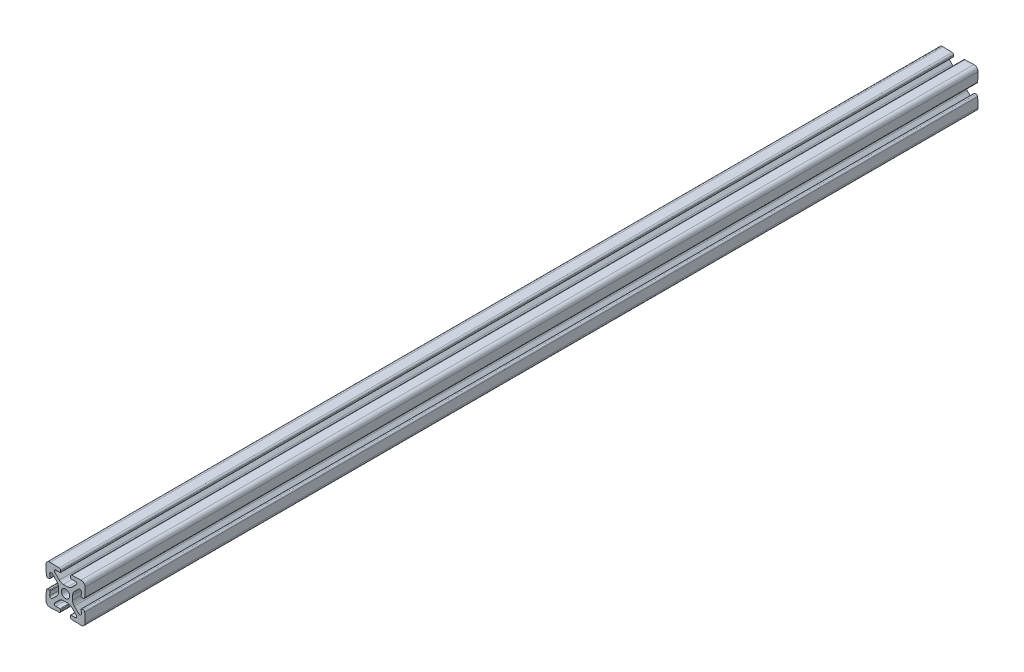
SolidWorks part; units mm, degrees
ref_plane "Front Plane" through (0, 0, 0) normal (0, 0, 1) x (1, 0, 0)
ref_plane "Top Plane" through (0, 0, 0) normal (0, 1, 0) x (1, 0, 0)
ref_plane "Right Plane" through (0, 0, 0) normal (1, 0, 0) x (0, 0, -1)
sketch "Sketch1" plane through (0, 0, 0) normal (0, 0, 1) x (1, 0, 0)
  line L0 (0, 0) -> (0, 10) construction
  line L1 (0, 0) -> (10, 0) construction
  line L2 (0, 0) -> (-10, 10) construction
  line L3 (-7.9302, 9.9988) -> (-3.2721, 9.8361)
  line L4 (-10, 10) -> (0, 10) construction
  line L6 (-2.8352, 8.0198) -> (-4.953, 8.0937)
  line L10 (0, 3.6) -> (-1.1022, 3.6)
  line L11 (-3.2236, 4.4787) -> (-5.5244, 6.7796)
  line L24 (0, 0) -> (-10, 0) construction
  line L25 (-10, 0) -> (0, 0) construction
  line L26 (0, 0) -> (0, -10) construction
  line L27 (-10, -10) -> (-10, 10) construction
  line L28 (0, 10) -> (10, 10) construction
  line L29 (-2.5249, 8.3091) -> (-2.5005, 9.0087)
  line L30 (-10, -10) -> (10, -10) construction
  arc A0 (-9.4142, 9.4142) -> (-7.9302, 9.9988) centre (-8, 8) cw
  arc A5 (-3.2721, 9.8361) -> (-2.5005, 9.0087) centre (-3.3, 9.0366) cw
  arc A6 (-1.1022, 3.6) -> (-3.2236, 4.4787) centre (-1.1022, 6.6) cw
  circle A16 centre (0, 0) radius 2.15
  arc A18 (-5.5244, 6.7796) -> (-4.953, 8.0937) centre (-4.9799, 7.3241) cw
  arc A20 (-2.8352, 8.0198) -> (-2.5249, 8.3091) centre (-2.8247, 8.3196) ccw
  point P15 (0, 0)
  point P42 (-2.3449, 3.6)
  point P80 (-10, 0)
  point P85 (0, -10)
  point P88 (0, -10)
  dimension "D11" = 2
  dimension "D15" = 3
  dimension "Center Hole Diameter" = 4.3
  dimension "D7" = 0.8
  dimension "D8" = 0.3
  dimension "D4" = 0.7701
  dimension "D1" = 45
  dimension "D2" = 2
  dimension "Rail Width" = 20
  dimension "T-Slot Depth" = 6.4
  dimension "D9" = 1.8
  dimension "Rail Height" = 20
  dimension "D23" = 7.2
  dimension "D5" = 11.5
  dimension "T-Slot Width" = 5
  dimension "D3" = 1.775
  dimension "D6" = 9.9598
sketch "Sketch2" plane through (0, 0, 0) normal (1, 0, 0) x (0, 0, -1)
  line L0 (-228.6, 0) -> (228.6, 0)
  line L1 (-228.6, -10) -> (-228.6, 10)
  line L2 (0, 0) -> (0, 10) construction
  line L3 (0, 0) -> (0, 10) construction
  line L4 (228.6, -10) -> (228.6, 10)
  point P0 (-198.6, 0)
  point P3 (0, 0)
  point P7 (198.6, 0)
  point P11 (-228.6, 0)
  point P14 (228.6, 0)
  dimension "D1" = 30
  dimension "Length" = 457.2
sketch "Sketch3" plane through (0, 0, 0) normal (0, 0, 1) x (1, 0, 0)
  line L0 (-2.5249, 8.3091) -> (-2.5005, 9.0087) construction
  line L1 (0, 0) -> (-10, 10) construction
  line L2 (0, 0) -> (-10, 10) construction
  line L5 (-7.9302, 9.9988) -> (-3.2721, 9.8361) construction
  line L6 (-2.8352, 8.0198) -> (-4.953, 8.0937) construction
  line L17 (-2.5249, 8.3091) -> (-2.5005, 9.0087)
  line L19 (-2.8352, 8.0198) -> (-4.953, 8.0937)
  line L20 (0, 0) -> (0, 10) construction
  line L21 (-3.6, 0) -> (-2.15, 0)
  line L22 (-3.6, 0) -> (-3.6, 1.1022)
  line L23 (-4.4787, 3.2236) -> (-6.7796, 5.5244)
  line L42 (-3.2236, 4.4787) -> (-5.5244, 6.7796) construction
  line L43 (0, 3.6) -> (-1.1022, 3.6) construction
  line L44 (-7.9302, 9.9988) -> (-3.2721, 9.8361)
  line L47 (-3.2236, 4.4787) -> (-5.5244, 6.7796)
  line L48 (0, 3.6) -> (-1.1022, 3.6)
  line L59 (0, 3.6) -> (0, 2.15)
  line L60 (-9.9988, 7.9302) -> (-9.8361, 3.2721)
  line L61 (-8.0198, 2.8352) -> (-8.0937, 4.953)
  line L62 (-8.3091, 2.5249) -> (-9.0087, 2.5005)
  arc A0 (-7.9302, 9.9988) -> (-9.4142, 9.4142) centre (-8, 8) ccw construction
  arc A1 (-2.8352, 8.0198) -> (-2.5249, 8.3091) centre (-2.8247, 8.3196) ccw construction
  arc A3 (-2.8352, 8.0198) -> (-2.5249, 8.3091) centre (-2.8247, 8.3196) ccw
  arc A5 (-7.9302, 9.9988) -> (-9.9988, 7.9302) centre (-8, 8) ccw
  circle A13 centre (0, 0) radius 2.15 construction
  arc A14 (0, 2.15) -> (-2.15, 0) centre (0, 0) ccw
  arc A15 (-4.4787, 3.2236) -> (-3.6, 1.1022) centre (-6.6, 1.1022) cw
  arc A16 (-8.0937, 4.953) -> (-6.7796, 5.5244) centre (-7.3241, 4.9799) cw
  arc A17 (-9.0087, 2.5005) -> (-9.8361, 3.2721) centre (-9.0366, 3.3) cw
  arc A18 (-8.0198, 2.8352) -> (-8.3091, 2.5249) centre (-8.3196, 2.8247) cw
  arc A36 (-2.5005, 9.0087) -> (-3.2721, 9.8361) centre (-3.3, 9.0366) ccw construction
  arc A38 (-4.953, 8.0937) -> (-5.5244, 6.7796) centre (-4.9799, 7.3241) ccw construction
  arc A39 (-3.2236, 4.4787) -> (-1.1022, 3.6) centre (-1.1022, 6.6) ccw construction
  arc A41 (-2.5005, 9.0087) -> (-3.2721, 9.8361) centre (-3.3, 9.0366) ccw
  arc A43 (-4.953, 8.0937) -> (-5.5244, 6.7796) centre (-4.9799, 7.3241) ccw
  arc A44 (-3.2236, 4.4787) -> (-1.1022, 3.6) centre (-1.1022, 6.6) ccw
extrude "Boss-Extrude1" add sketch "Sketch3" along normal mid plane 457.2
pattern_circular "CirPattern1" count 4 over 360 about axis through (0, 0, 0) along (0, 0, 1) of "Boss-Extrude1"
ref_plane "Contact Plane 1" through (0, 10, 0) normal (0, 1, 0) x (1, 0, 0)
ref_plane "Contact Plane 2" through (10, 0, 0) normal (1, 0, 0) x (0, 0, -1)
ref_plane "Contact Plane 3" through (0, -10, 0) normal (0, -1, 0) x (-1, 0, 0)
ref_plane "Contact Plane 4" through (-10, 0, 0) normal (-1, 0, 0) x (0, 0, 1)
equation "\"D1@Sketch2\"=\"Rail Width@Sketch1\"*1.5"
equation "\"D1@Boss-Extrude1\" = \"Length@Sketch2\""
